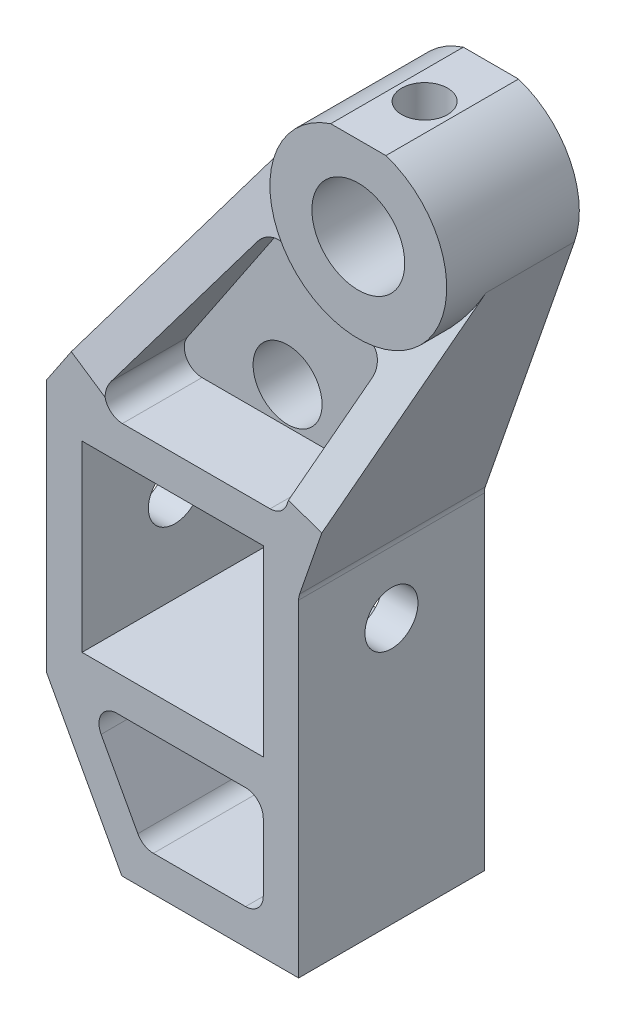
SolidWorks part; units mm, degrees
ref_plane "Front Plane" through (0, 0, 0) normal (0, 0, 1) x (1, 0, 0)
ref_plane "Top Plane" through (0, 0, 0) normal (0, 1, 0) x (1, 0, 0)
ref_plane "Right Plane" through (0, 0, 0) normal (1, 0, 0) x (0, 0, -1)
sketch "Sketch1" plane through (0, 0, 0) normal (0, 0, 1) x (1, 0, 0)
  line L0 (-4.75, -29.65) -> (-25.25, -50.35) construction
  line L1 (-25.25, -29.65) -> (-4.75, -29.65)
  line L2 (-25.25, -29.65) -> (-25.25, -50.35)
  line L3 (-25.25, -50.35) -> (-4.75, -50.35)
  line L4 (-4.75, -29.65) -> (-4.75, -50.35)
  line L5 (-29.25, -25.65) -> (-29.25, -54.35)
  line L6 (-29.25, -25.65) -> (-8.3043, 5.5712)
  line L7 (-29.25, -54.35) -> (-20.75, -70)
  line L8 (-20.75, -70) -> (-0.75, -70)
  line L9 (-0.75, -70) -> (-0.75, -32.65)
  line L10 (-3.1225, 9.5) -> (3.1225, 9.5)
  line L11 (-0.75, -32.65) -> (9.4469, -3.2798)
  circle A0 centre (0, 0) radius 5.25
  circle A1 centre (-15, -40) radius 5 construction
  arc A2 (9.4469, -3.2798) -> (3.1225, 9.5) centre (0, 0) ccw
  arc A3 (-3.1225, 9.5) -> (-8.3043, 5.5712) centre (0, 0) ccw
  circle A4 centre (-11, -21.5) radius 3.9
  dimension "D3" = 10.5
  dimension "D4" = 10
  dimension "D8" = 20
  dimension "D18" = 7.8
  dimension "D1" = 40
  dimension "D2" = 15
  dimension "D5" = 20.7
  dimension "D6" = 20.5
  dimension "D7" = 4
  dimension "D9" = 4
  dimension "D10" = 20
  dimension "D11" = 30
  dimension "D12" = 3
  dimension "D13" = 9.5
  dimension "D14" = 4
  dimension "D15" = 4
  dimension "D16" = 18.5
  dimension "D17" = 4
extrude "Boss-Extrude1" add sketch "Sketch1" along normal blind 4
sketch "Sketch2" plane through (0, 0, 4) normal (0, 0, 1) x (1, 0, 0)
  line L0 (3.1225, 9.5) -> (-3.1225, 9.5) construction
  line L1 (3.1225, 9.5) -> (-3.1225, 9.5)
  arc A0 (-3.1225, 9.5) -> (-8.3043, 5.5712) centre (0, 0) ccw construction
  arc A1 (-3.1225, 9.5) -> (3.1225, 9.5) centre (0, 0) ccw
  circle A3 centre (0, 0) radius 5.25 construction
  circle A4 centre (0, 0) radius 5.25
extrude "Boss-Extrude2" add sketch "Sketch2" along normal blind 11
sketch "Sketch3" plane through (0, 0, 4) normal (0, 0, 1) x (1, 0, 0)
  line L1 (-25.25, -29.65) -> (-4.75, -29.65) construction
  line L2 (-4.75, -29.65) -> (-4.75, -50.35) construction
  line L3 (-4.75, -50.35) -> (-25.25, -50.35) construction
  line L5 (-20.75, -70) -> (-0.75, -70) construction
  line L6 (-29.25, -54.35) -> (-20.75, -70) construction
  line L7 (-25.25, -29.65) -> (-25.25, -50.35)
  line L8 (-25.25, -29.65) -> (-4.75, -29.65)
  line L9 (-4.75, -29.65) -> (-4.75, -50.35)
  line L10 (-4.75, -50.35) -> (-25.25, -50.35)
  line L11 (-29.25, -25.65) -> (-29.25, -54.35)
  line L12 (-20.75, -70) -> (-0.75, -70)
  line L13 (-29.25, -54.35) -> (-20.75, -70)
  line L14 (-29.25, -25.65) -> (-0.75, -25.65)
  line L15 (-0.75, -25.65) -> (-0.75, -70)
  line L16 (-6.75, -54.35) -> (-21.3359, -54.35)
  line L17 (-23.0934, -57.3046) -> (-18.9384, -64.9546)
  line L18 (-17.1809, -66) -> (-6.75, -66)
  line L22 (-4.75, -56.35) -> (-4.75, -64)
  arc A0 (-18.9384, -64.9546) -> (-17.1809, -66) centre (-17.1809, -64) ccw
  arc A1 (-21.3359, -54.35) -> (-23.0934, -57.3046) centre (-21.3359, -56.35) ccw
  arc A2 (-6.75, -54.35) -> (-4.75, -56.35) centre (-6.75, -56.35) cw
  arc A3 (-4.75, -64) -> (-6.75, -66) centre (-6.75, -64) cw
  dimension "D4" = 2
  dimension "D5" = 2
  dimension "D1" = 4
  dimension "D3" = 4
extrude "Boss-Extrude3" add sketch "Sketch3" along normal blind 17
sketch "Sketch4" plane through (-8.3043, 5.5712, 0) normal (-0.8304, 0.5571, 0) x (0, 0, 1)
  line L0 (4, -37.5963) -> (21, -37.5963)
  line L1 (21, -37.5963) -> (21, -32.5963)
  line L2 (21, -21.7184) -> (21, -37.5963) construction
  line L3 (21, -32.5963) -> (12, 0)
  line L4 (12, 0) -> (4, 0)
  line L5 (4, 0) -> (4, -37.5963)
  line L6 (15, -10) -> (15, 10) construction
  dimension "D1" = 5
  dimension "D2" = 3
extrude "Boss-Extrude4" add sketch "Sketch4" against normal blind 4
sketch "Sketch6" plane through (9.4469, -3.2798, 0) normal (0.9447, -0.328, 0) x (0, 0, -1)
  line L0 (-4, -31.09) -> (-21, -31.09)
  line L1 (-21, -31.09) -> (-21, -23.09)
  line L2 (-21, -23.09) -> (-10, 0)
  line L3 (-10, 0) -> (-4, 0)
  line L4 (-4, 0) -> (-4, -31.09)
  line L5 (-15, 10) -> (-15, -10) construction
  line L6 (-21, -66.3739) -> (-21, -24.4772) construction
  dimension "D1" = 8
  dimension "D2" = 5
extrude "Boss-Extrude6" add sketch "Sketch6" against normal blind 4
fillet "Fillet8" radius 2 5 edges at (-24.4332, -25.65, 12.5) (-2.5539, -25.65, 12.5) (3.0443, -9.5254, 8.9056) (-9.4396, -3.3007, 9.1044) (-0.75, -32.65, 10.5)
sketch "Sketch7" plane through (0, 9.5, 0) normal (0, 1, 0) x (1, 0, 0)
  line L0 (0, 0) -> (0, -15) construction
  line L1 (3.1225, 0) -> (-3.1225, 0) construction
  line L2 (3.1225, -15) -> (-3.1225, -15) construction
  circle A0 centre (0, -7.5) radius 2.6
  dimension "D1" = 5.2
extrude "Cut-Extrude1" cut sketch "Sketch7" against normal blind 6
sketch "Sketch9" plane through (-4.75, 0, 0) normal (-1, 0, 0) x (0, 0, 1)
  line L0 (0, -29.65) -> (21, -50.35) construction
  circle A0 centre (10.5, -40) radius 3
  dimension "D1" = 6
extrude "Cut-Extrude2" cut sketch "Sketch9" against normal through all and the other way through all
sketch "Sketch10" plane through (0, 0, 4) normal (0, 0, 1) x (1, 0, 0)
  line L3 (-11.2857, -6.0525) -> (-22.3439, -22.5358)
  line L4 (-20.6831, -25.65) -> (-3.9767, -25.65)
  line L5 (-2.0873, -24.306) -> (1.9575, -12.6558)
  line L6 (-11.2857, -6.0525) -> (-22.3439, -22.5358)
  line L7 (-20.6831, -25.65) -> (-3.9767, -25.65)
  line L8 (-2.0873, -24.306) -> (1.9575, -12.6558)
  circle A1 centre (-11, -21.5) radius 3.9 construction
  circle A2 centre (-11, -21.5) radius 3.9
  arc A7 (-22.3439, -22.5358) -> (-20.6831, -25.65) centre (-20.6831, -23.65) ccw
  arc A8 (-3.9767, -25.65) -> (-2.0873, -24.306) centre (-3.9767, -23.65) ccw
  arc A9 (1.9575, -12.6558) -> (0.0567, -9.9998) centre (0.0681, -11.9998) ccw
  arc A10 (-8.0207, -5.9723) -> (0.0567, -9.9998) centre (0, 0) ccw
  arc A11 (-8.0207, -5.9723) -> (-11.2857, -6.0525) centre (-9.6248, -7.1668) ccw
  arc A12 (-22.3439, -22.5358) -> (-20.6831, -25.65) centre (-20.6831, -23.65) ccw
  arc A13 (-3.9767, -25.65) -> (-2.0873, -24.306) centre (-3.9767, -23.65) ccw
  arc A14 (1.9575, -12.6558) -> (0.0567, -9.9998) centre (0.0681, -11.9998) ccw
  arc A15 (-8.0207, -5.9723) -> (0.0567, -9.9998) centre (0, 0) ccw
  arc A16 (-8.0207, -5.9723) -> (-11.2857, -6.0525) centre (-9.6248, -7.1668) ccw
  dimension "D1" = 0
extrude "Boss-Extrude7" add sketch "Sketch10" along normal blind 8
